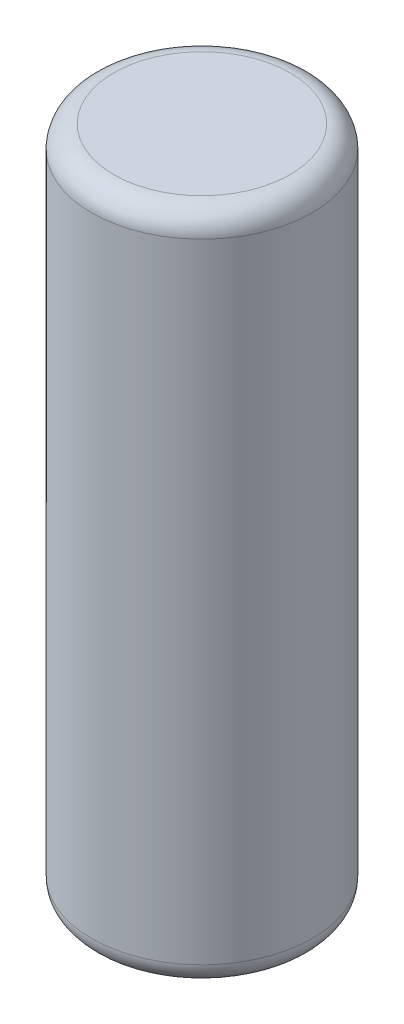
SolidWorks part; units mm, degrees
ref_plane "Front Plane" through (0, 0, 0) normal (0, 0, 1) x (1, 0, 0)
ref_plane "Top Plane" through (0, 0, 0) normal (0, 1, 0) x (1, 0, 0)
ref_plane "Right Plane" through (0, 0, 0) normal (1, 0, 0) x (0, 0, -1)
sketch "Sketch1" plane through (0, 0, 0) normal (0, 1, 0) x (1, 0, 0)
  circle A0 centre (0, 0) radius 10
extrude "Boss-Extrude1" add sketch "Sketch1" along normal blind 61
fillet "Fillet1" radius 2 2 edges at (0, 0, 10) (0, 61, 10)
